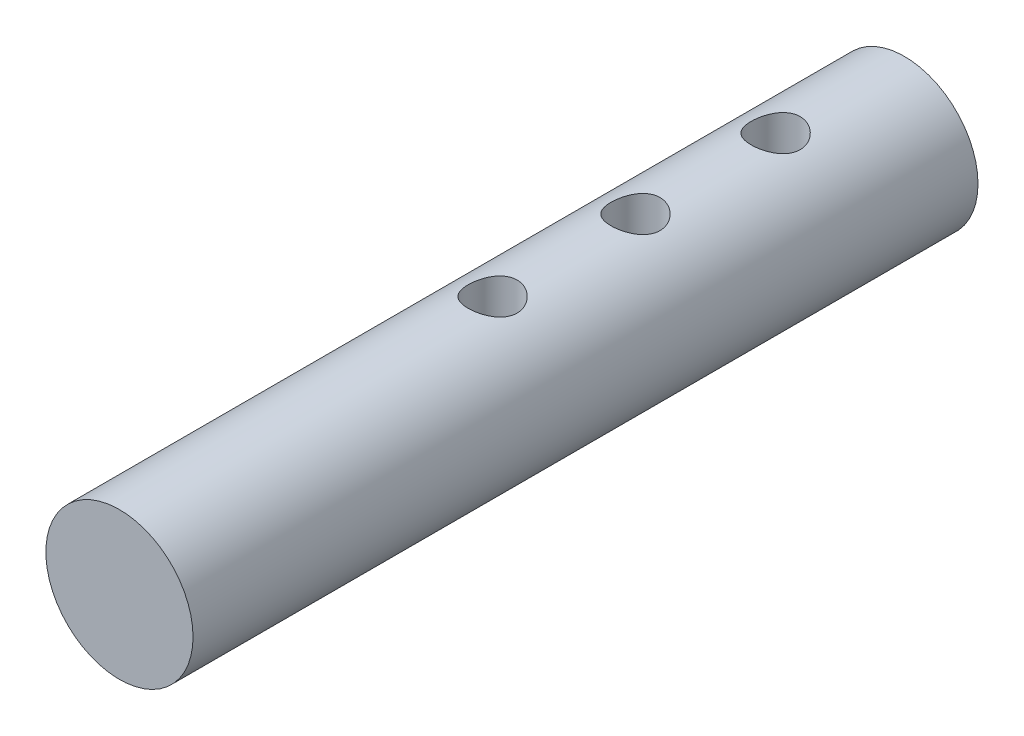
SolidWorks part; units mm, degrees
material "1060 Alloy"
ref_plane "Front Plane" through (0, 0, 0) normal (0, 0, 1) x (1, 0, 0)
ref_plane "Top Plane" through (0, 0, 0) normal (0, 1, 0) x (1, 0, 0)
ref_plane "Right Plane" through (0, 0, 0) normal (1, 0, 0) x (0, 0, -1)
sketch "Sketch1" plane through (0, 0, 0) normal (0, 0, 1) x (1, 0, 0)
  circle A0 centre (0, 0) radius 19.05
  dimension "D1" = 38.1
extrude "Boss-Extrude1" add sketch "Sketch1" along normal blind 203.2
hole_wizard "#97 (0.0059) Diameter Hole1" positions "3DSketch2" profile "Sketch3" hole size "#97" standard "ANSI Inch"
sketch3d "3DSketch2"
  point P0 (0, 19.05, 33.3448)
  point P2 (0, 19.05, 69.6203)
  point P3 (0, 19.05, 106.6117)
sketch "Sketch3" plane through (0, 19.05, 33.3448) normal (1, 0, 0) x (0, 0, 1)
  line L0 (0, 0) -> (0, 213.8735)
  line L1 (0, 213.8735) -> (6.35, 210.058)
  line L2 (6.35, 210.058) -> (6.35, 0)
  line L5 (6.35, 0) -> (0, 0)
  line L10 (0, 213.8735) -> (-6.35, 210.058) construction
  line L11 (0, -6.35) -> (0, 107.95) construction
  dimension "Hole Dia." = 12.7
  dimension "Hole Depth" = 210.058
  dimension "Drill Angle" = 118
